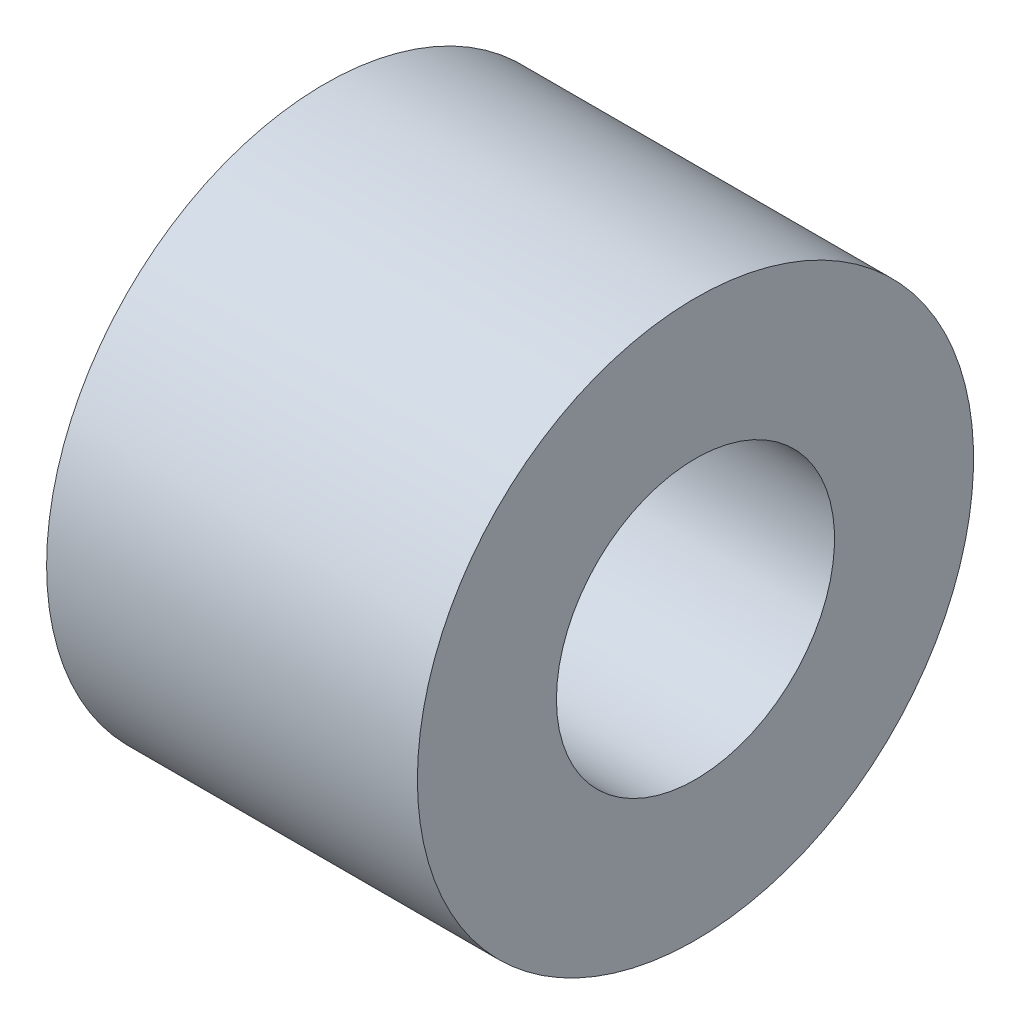
SolidWorks part; units mm, degrees
ref_plane "Face" through (0, 0, 0) normal (0, 0, 1) x (1, 0, 0)
ref_plane "Dessus" through (0, 0, 0) normal (0, 1, 0) x (1, 0, 0)
ref_plane "Droite" through (0, 0, 0) normal (1, 0, 0) x (0, 0, -1)
sketch "Esquisse1" plane through (0, 0, 0) normal (0, 0, 1) x (1, 0, 0)
  line L0 (-47.5268, 0) -> (47.5268, 0) construction
  line L1 (-23.9074, 7.5) -> (-13.9074, 7.5)
  line L2 (-13.9074, 7.5) -> (-13.9074, 3.75)
  line L3 (-13.9074, 3.75) -> (-23.9074, 3.75)
  line L4 (-23.9074, 3.75) -> (-23.9074, 7.5)
revolve "Révolution1" add sketch "Esquisse1" angle 360 about L0
